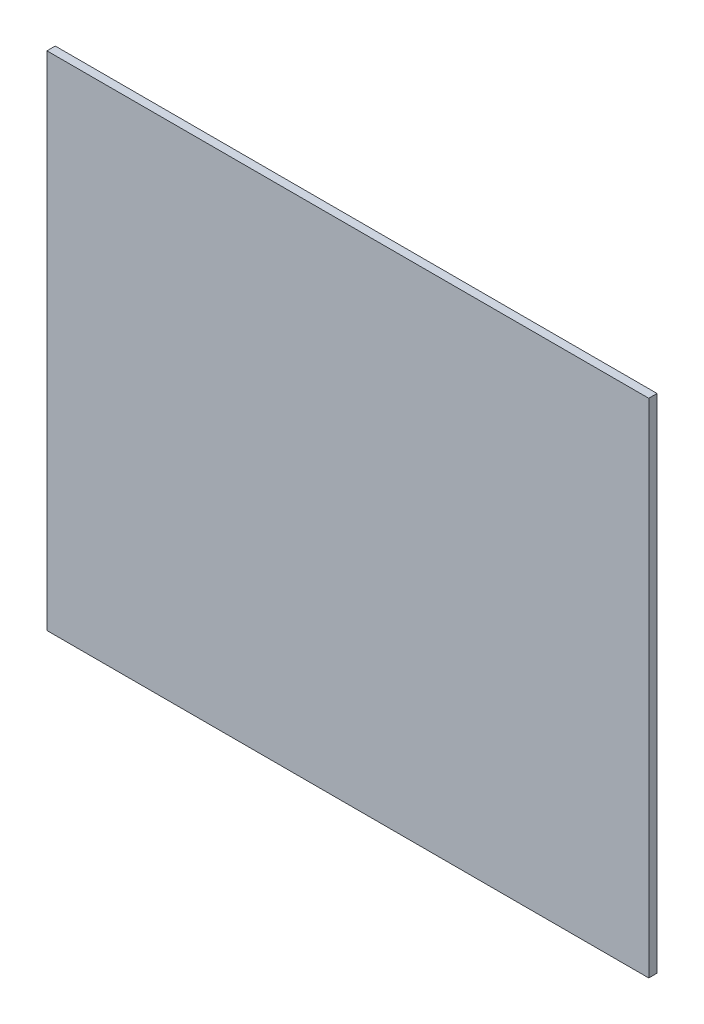
SolidWorks part; units mm, degrees
material "Glass"
ref_plane "Front Plane" through (0, 0, 0) normal (0, 0, 1) x (1, 0, 0)
ref_plane "Top Plane" through (0, 0, 0) normal (0, 1, 0) x (1, 0, 0)
ref_plane "Right Plane" through (0, 0, 0) normal (1, 0, 0) x (0, 0, -1)
sketch "Sketch3" plane through (0, 0, 0) normal (0, 0, 1) x (1, 0, 0)
  line L0 (0, 0) -> (0, 151) construction
  dimension "D1" = 151
sketch "Sketch1" plane through (0, 0, 0) normal (0, 1, 0) x (1, 0, 0)
  line L0 (0, -21) -> (0, 21) construction
  line L2 (-90.5, -21) -> (90.5, -21)
  line L3 (-90.5, -21) -> (-90.5, -23.5)
  line L4 (-90.5, -23.5) -> (90.5, -23.5)
  line L5 (90.5, -21) -> (90.5, -23.5)
  line L6 (-90.5, 21) -> (90.5, 21)
  line L7 (-90.5, 21) -> (-90.5, 23.5)
  line L8 (-90.5, 23.5) -> (90.5, 23.5)
  line L9 (90.5, 21) -> (90.5, 23.5)
  point P4 (0, 0)
  dimension "D1" = 42
  dimension "D2" = 181
  dimension "D3" = 2.5
extrude "Boss-Extrude1" add sketch "Sketch1" along normal up to vertex (151 mm away) contours L5 L2 L3 L4 up to point (0, 151, 0)
equation "\"glass_width\"= 181"
equation "\"glass_height\"= 151"
equation "\"glass_thickness\"= 2.5"
equation "\"brood_space\"= 42"
equation "\"D3@Sketch1\"=\"glass_thickness\""
equation "\"D2@Sketch1\"=\"glass_width\""
equation "\"D1@Sketch3\"=\"glass_height\""
